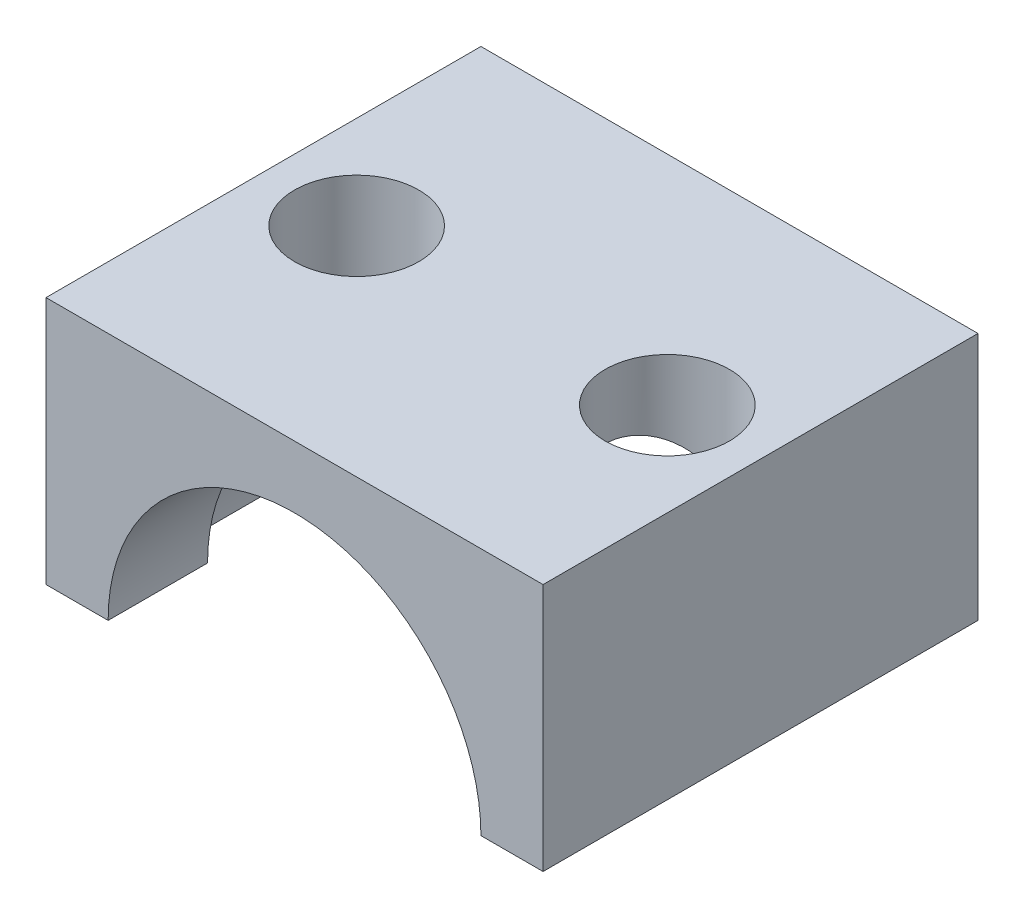
SolidWorks part; units mm, degrees
ref_plane "Plan de face" through (0, 0, 0) normal (0, 0, 1) x (1, 0, 0)
ref_plane "Plan de dessus" through (0, 0, 0) normal (0, 1, 0) x (1, 0, 0)
ref_plane "Plan de droite" through (0, 0, 0) normal (1, 0, 0) x (0, 0, -1)
sketch "Esquisse1" plane through (0, 0, 0) normal (0, 0, 1) x (1, 0, 0)
  line L0 (8, 0) -> (6, 0)
  line L1 (8, 8) -> (8, 0)
  line L3 (-6, 0) -> (-8, 0)
  line L4 (-8, 0) -> (-8, 8)
  line L5 (8, 8) -> (-8, 8)
  arc A0 (6, 0) -> (-6, 0) centre (0, 0) ccw
extrude "Extrusion1" add sketch "Esquisse1" along normal blind 14
ref_plane "Plan1" through (0, 0, 7) normal (0, 0, 1) x (1, 0, 0)
sketch "Esquisse3" plane through (0, 0, 7) normal (0, 0, 1) x (1, 0, 0)
  circle A0 centre (0, -0.3999) radius 7
extrude "Extrusion2" cut sketch "Esquisse3" against normal blind 3.8 and the other way blind 3.8
sketch "Esquisse4" plane through (0, 8, 0) normal (0, 1, 0) x (1, 0, 0)
  line L0 (-8, -7) -> (8, -7) construction
  line L2 (-8, -14) -> (-8, 0) construction
  line L3 (8, -14) -> (8, 0) construction
  circle A1 centre (-5, -7) radius 2
  circle A2 centre (5, -7) radius 2
extrude "Extrusion3" cut sketch "Esquisse4" against normal through all
